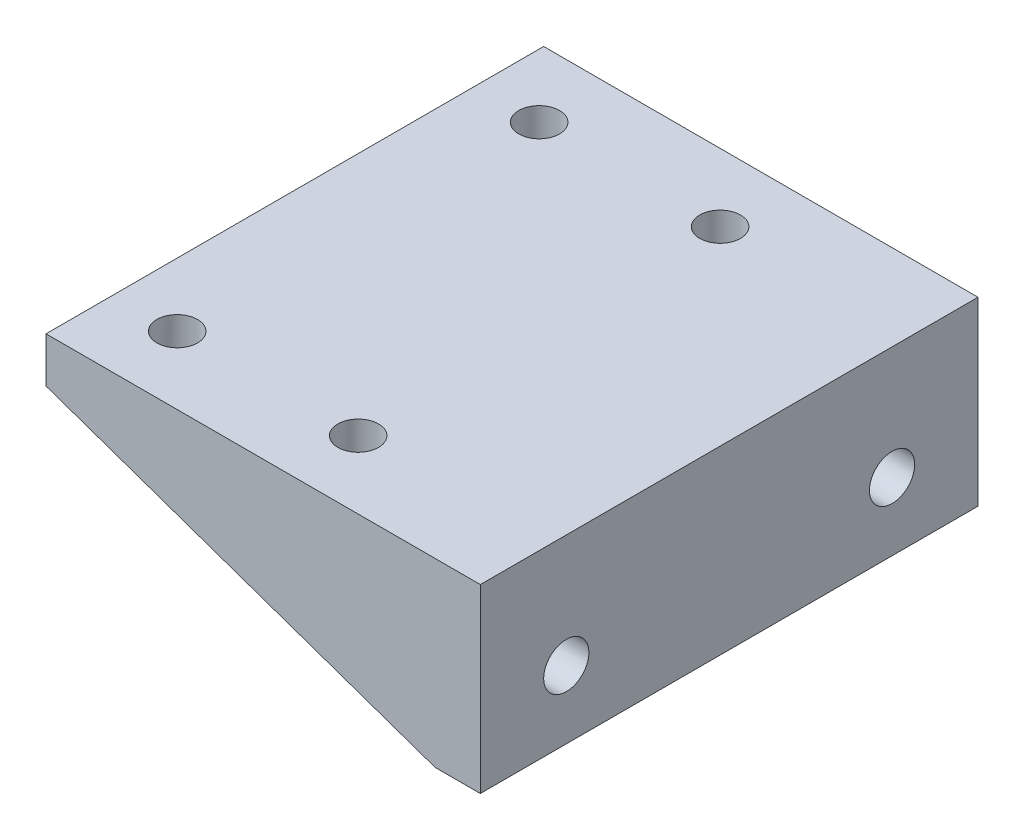
SolidWorks part; units mm, degrees
ref_plane "Front Plane" through (0, 0, 0) normal (0, 0, 1) x (1, 0, 0)
ref_plane "Top Plane" through (0, 0, 0) normal (0, 1, 0) x (1, 0, 0)
ref_plane "Right Plane" through (0, 0, 0) normal (1, 0, 0) x (0, 0, -1)
sketch "Sketch1" plane through (0, 0, 0) normal (0, 1, 0) x (1, 0, 0)
  line L1 (15, -27.5) -> (-15, -27.5)
  line L2 (15, -27.5) -> (15, 27.5)
  line L3 (15, 27.5) -> (-15, 27.5)
  line L4 (-15, -27.5) -> (-15, 27.5)
  line L5 (15, -27.5) -> (-15, 27.5) construction
  line L6 (15, 27.5) -> (-15, -27.5) construction
  point P0 (0, 0)
  dimension "D1" = 30
  dimension "D2" = 55
extrude "Boss-Extrude1" add sketch "Sketch1" along normal blind 5
sketch "Sketch4" plane through (15, 0, 0) normal (1, 0, 0) x (0, 0, -1)
  line L1 (-27.5, 5) -> (27.5, 5)
  line L2 (-27.5, 5) -> (-27.5, 0)
  line L3 (-27.5, 0) -> (27.5, 0)
  line L4 (27.5, 5) -> (27.5, 0)
extrude "Boss-Extrude2" add sketch "Sketch4" along normal blind 18
sketch "Sketch5" plane through (33, 0, 0) normal (1, 0, 0) x (0, 0, -1)
  line L0 (-27.5, 5) -> (-27.5, 0) construction
  line L1 (27.5, 5) -> (-27.5, 5)
  line L2 (27.5, 5) -> (27.5, -15)
  line L3 (27.5, -15) -> (-27.5, -15)
  line L4 (-27.5, 5) -> (-27.5, -15)
  point P7 (-27.5, 2.5)
  dimension "D1" = 20
  dimension "D2" = 0
extrude "Boss-Extrude3" add sketch "Sketch5" against normal blind 5
sketch "Sketch6" plane through (33, 0, 0) normal (1, 0, 0) x (0, 0, -1)
  line L1 (0, 2.75) -> (0, -2.75) construction
  circle A0 centre (18, -7.5) radius 2.5
  circle A1 centre (-18, -7.5) radius 2.5
  dimension "D1" = 18
extrude "Cut-Extrude3" cut sketch "Sketch6" against normal blind 5
sketch "Sketch7" plane through (0, 0, 27.5) normal (0, 0, 1) x (1, 0, 0)
  line L0 (28, -15) -> (-15, 0)
  line L1 (-15, 0) -> (28, 0)
  line L2 (28, 0) -> (28, -15)
extrude "Boss-Extrude4" add sketch "Sketch7" against normal blind 3
mirror "Mirror1" about plane through (0, 0, 0) normal (0, 0, 1) of "Boss-Extrude4"
sketch "Sketch8" plane through (0, 0, 0) normal (0, -1, 0) x (1, 0, 0)
  circle A0 centre (-8, 20) radius 2.25
  circle A1 centre (-8, -20) radius 2.25
  circle A2 centre (12, 20) radius 2.25
  circle A3 centre (12, -20) radius 2.25
  dimension "D1" = 20
  dimension "D2" = 20
  dimension "D3" = 8
  dimension "D4" = 0
  dimension "D6" = 20
  dimension "D5" = 2
extrude "Cut-Extrude4" cut sketch "Sketch8" against normal blind 10
